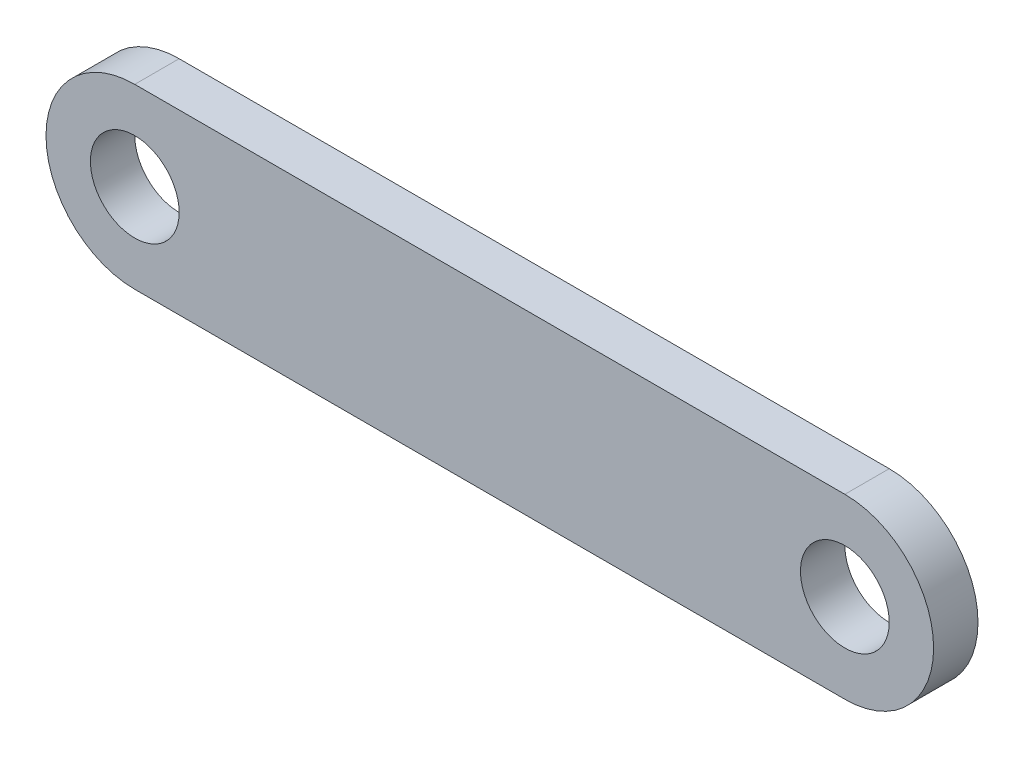
SolidWorks part; units mm, degrees
ref_plane "Front Plane" through (0, 0, 0) normal (0, 0, 1) x (1, 0, 0)
ref_plane "Top Plane" through (0, 0, 0) normal (0, 1, 0) x (1, 0, 0)
ref_plane "Right Plane" through (0, 0, 0) normal (1, 0, 0) x (0, 0, -1)
sketch "Sketch1" plane through (0, 0, 0) normal (0, 0, 1) x (1, 0, 0)
  line L0 (0, 6.35) -> (50.8, 6.35)
  line L1 (0, -6.35) -> (50.8, -6.35)
  arc A0 (0, 6.35) -> (0, -6.35) centre (0, 0) ccw
  arc A1 (50.8, -6.35) -> (50.8, 6.35) centre (50.8, 0) ccw
  circle A2 centre (0, 0) radius 3.175
  circle A3 centre (50.8, 0) radius 3.175
  dimension "D1" = 12.7
  dimension "D4" = 6.35
  dimension "D5" = 6.35
  dimension "D2" = 50.8
  dimension "D3" = 50.8
extrude "Boss-Extrude1" add sketch "Sketch1" along normal blind 3.175
